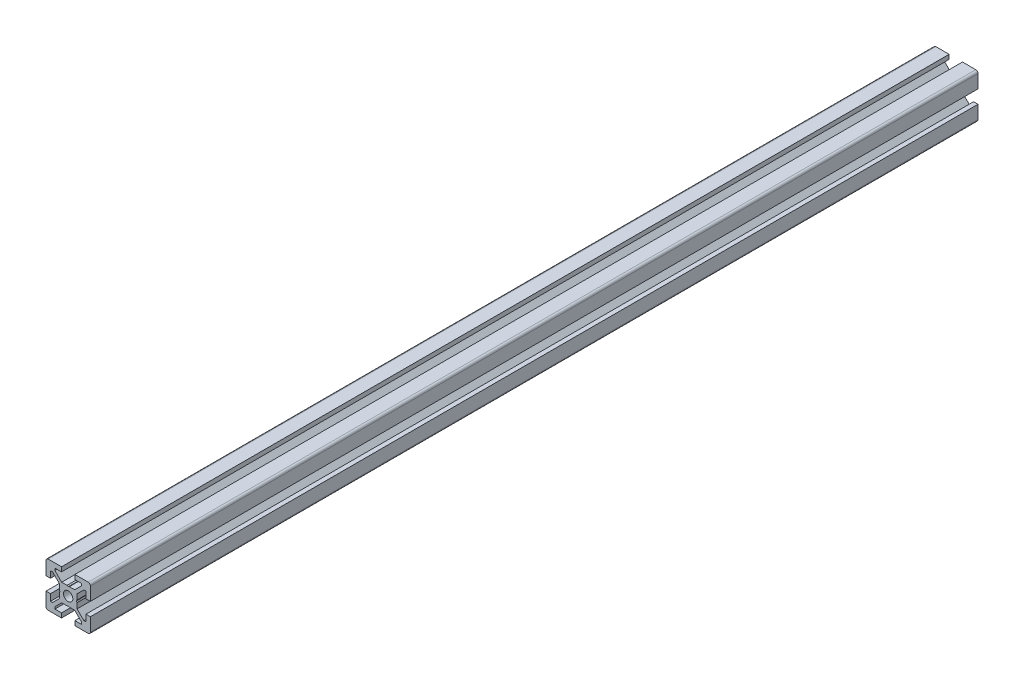
SolidWorks part; units mm, degrees
ref_plane "Front Plane" through (0, 0, 0) normal (0, 0, 1) x (1, 0, 0)
ref_plane "Top Plane" through (0, 0, 0) normal (0, 1, 0) x (1, 0, 0)
ref_plane "Right Plane" through (0, 0, 0) normal (1, 0, 0) x (0, 0, -1)
ref_plane "Plane1" through (0, 0, -400) normal (0, 0, -1) x (-1, 0, 0)
sketch "Sketch1" plane through (0, 0, -400) normal (0, 0, -1) x (-1, 0, 0)
  line L0 (10, -3) -> (8, -3)
  line L1 (8, -3) -> (8, -6)
  line L2 (8, -6) -> (7.0607, -6)
  line L3 (7.0607, -6) -> (4, -2.9393)
  line L4 (4, -2.9393) -> (4, -0.5196)
  line L5 (4, -0.5196) -> (3.7, 0)
  line L6 (3.7, 0) -> (4, 0.5196)
  line L7 (4, 0.5196) -> (4, 2.9393)
  line L8 (4, 2.9393) -> (7.0607, 6)
  line L9 (7.0607, 6) -> (8, 6)
  line L10 (8, 6) -> (8, 3)
  line L11 (8, 3) -> (10, 3)
  line L12 (10, 3) -> (10, 9)
  line L13 (9, 10) -> (3, 10)
  line L14 (3, 10) -> (3, 8)
  line L15 (3, 8) -> (6, 8)
  line L16 (6, 8) -> (6, 7.0607)
  line L17 (6, 7.0607) -> (2.9393, 4)
  line L18 (2.9393, 4) -> (0.5196, 4)
  line L19 (0.5196, 4) -> (0, 3.7)
  line L20 (0, 3.7) -> (-0.5196, 4)
  line L21 (-0.5196, 4) -> (-2.9393, 4)
  line L22 (-2.9393, 4) -> (-6, 7.0607)
  line L23 (-6, 7.0607) -> (-6, 8)
  line L24 (-6, 8) -> (-3, 8)
  line L25 (-3, 8) -> (-3, 10)
  line L26 (-3, 10) -> (-9, 10)
  line L27 (-10, 9) -> (-10, 3)
  line L28 (-10, 3) -> (-8, 3)
  line L29 (-8, 3) -> (-8, 6)
  line L30 (-8, 6) -> (-7.0607, 6)
  line L31 (-7.0607, 6) -> (-4, 2.9393)
  line L32 (-4, 2.9393) -> (-4, 0.5196)
  line L33 (-4, 0.5196) -> (-3.7, 0)
  line L34 (-3.7, 0) -> (-4, -0.5196)
  line L35 (-4, -0.5196) -> (-4, -2.9393)
  line L36 (-4, -2.9393) -> (-7.0607, -6)
  line L37 (-7.0607, -6) -> (-8, -6)
  line L38 (-8, -6) -> (-8, -3)
  line L39 (-8, -3) -> (-10, -3)
  line L40 (-10, -3) -> (-10, -9)
  line L41 (-9, -10) -> (-3, -10)
  line L42 (-3, -10) -> (-3, -8)
  line L43 (-3, -8) -> (-6, -8)
  line L44 (-6, -8) -> (-6, -7.0607)
  line L45 (-6, -7.0607) -> (-2.9393, -4)
  line L46 (-2.9393, -4) -> (-0.5196, -4)
  line L47 (-0.5196, -4) -> (0, -3.7)
  line L48 (0, -3.7) -> (0.5196, -4)
  line L49 (0.5196, -4) -> (2.9393, -4)
  line L50 (2.9393, -4) -> (6, -7.0607)
  line L51 (6, -7.0607) -> (6, -8)
  line L52 (6, -8) -> (3, -8)
  line L53 (3, -8) -> (3, -10)
  line L54 (3, -10) -> (9, -10)
  line L55 (10, -9) -> (10, -3)
  circle A0 centre (0, 0) radius 2.1
  arc A1 (10, 9) -> (9, 10) centre (9, 9) ccw
  arc A2 (-9, 10) -> (-10, 9) centre (-9, 9) ccw
  arc A3 (-10, -9) -> (-9, -10) centre (-9, -9) ccw
  arc A4 (9, -10) -> (10, -9) centre (9, -9) ccw
extrude "Boss-Extrude1" add sketch "Sketch1" against normal blind 400
hole_wizard "M5x0.8 Tapped Hole1" positions "Sketch2" profile "Sketch4" tap size "M5x0.8" standard "ANSI Metric"
sketch "Sketch2" plane through (0, 0, 0) normal (0, 0, 1) x (1, 0, 0)
  point P0 (0, 0)
sketch "Sketch4" plane through (0, 0, 0) normal (1, 0, 0) x (0, -1, 0)
  line L0 (0, 0) -> (0, 15.2618)
  line L1 (0, 15.2618) -> (2.1, 14)
  line L2 (2.1, 14) -> (2.1, 0)
  line L5 (2.1, 0) -> (0, 0)
  line L10 (0, 15.2618) -> (-2.1, 14) construction
  line L11 (0, -6.35) -> (0, 107.95) construction
  dimension "Tap Drill Dia." = 4.2
  dimension "Tap Drill Depth" = 14
  dimension "Drill Angle" = 118
hole_wizard "M5x0.8 Tapped Hole2" positions "Sketch5" profile "Sketch6" tap size "M5x0.8" standard "ANSI Metric"
sketch "Sketch5" plane through (0, 0, -400) normal (0, 0, -1) x (-1, 0, 0)
  point P0 (0, 0)
sketch "Sketch6" plane through (0, 0, -400) normal (1, 0, 0) x (0, 1, 0)
  line L0 (0, 0) -> (0, 15.2618)
  line L1 (0, 15.2618) -> (2.1, 14)
  line L2 (2.1, 14) -> (2.1, 0)
  line L5 (2.1, 0) -> (0, 0)
  line L10 (0, 15.2618) -> (-2.1, 14) construction
  line L11 (0, -6.35) -> (0, 107.95) construction
  dimension "Tap Drill Dia." = 4.2
  dimension "Tap Drill Depth" = 14
  dimension "Drill Angle" = 118
